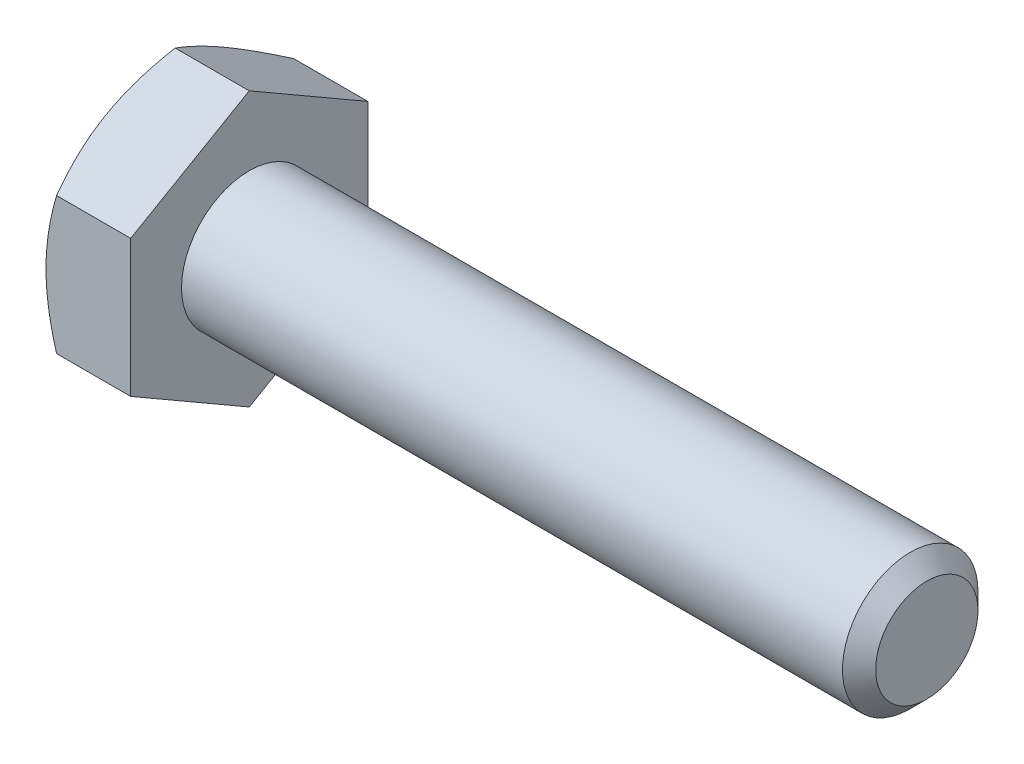
SolidWorks part; units mm, degrees
material "Alloy Steel"
ref_plane "Front Plane" through (0, 0, 0) normal (0, 0, 1) x (1, 0, 0)
ref_plane "Top Plane" through (0, 0, 0) normal (0, 1, 0) x (1, 0, 0)
ref_plane "Right Plane" through (0, 0, 0) normal (1, 0, 0) x (0, 0, -1)
sketch "Sketch1" plane through (0, 0, 0) normal (0, 0, 1) x (1, 0, 0)
  line L0 (-17.8594, 0) -> (17.8594, 0) construction
  line L1 (17.8594, 3.175) -> (17.8594, -3.175) construction
  line L2 (-13.8906, 5.5562) -> (-13.8906, -5.5562) construction
  line L3 (-17.8594, 5.5562) -> (-17.8594, -5.5562) construction
  point P9 (-13.8906, 0)
  point P10 (13.4144, -3.175)
  dimension "D1" = 4.445
  dimension "Screw Dia" = 6.35
  dimension "Hex" = 11.1125
  dimension "Head Ht" = 3.9688
  dimension "Screw Lenght" = 31.75
ref_plane "Plane2" through (17.8594, 0, 0) normal (1, 0, 0) x (0, 0, -1)
sketch "Sketch5" plane through (17.8594, 0, 0) normal (1, 0, 0) x (0, 0, -1)
  circle A0 centre (0, 0) radius 3.175
extrude "Boss-Extrude3" add sketch "Sketch5" against normal up to vertex (31.75 mm away) up to point (-13.8906, 0, 0)
sketch "Sketch9" plane through (17.8594, 0, 0) normal (1, 0, 0) x (0, 0, -1)
  circle A1 centre (0, 0) radius 3.175
  circle A2 centre (0, 0) radius 3.175
  dimension "D1" = 0
curve "Helix/Spiral1" pitch 1.27 height 33.02 turns 26 parameters "Pitch"=1.27
chamfer "Chamfer1" distance 0.7772 angle 45 1 edges at (17.8594, 0, -3.175)
sketch "Sketch10" plane through (0, 0, 0) normal (0, 0, 1) x (1, 0, 0)
  line L0 (17.8594, 3.175) -> (18.3356, 2.3501)
  line L1 (18.3356, 2.3501) -> (18.4944, 2.3501)
  line L2 (18.4944, 2.3501) -> (18.9706, 3.175)
  line L3 (17.8594, 3.175) -> (18.9706, 3.175)
  line L4 (18.415, 3.175) -> (18.415, 2.3501) construction
  line L5 (18.0975, 2.7626) -> (18.7325, 2.7626) construction
  dimension "D1" = 60
  dimension "D2" = 0.1588
  dimension "D3" = 0.635
sketch "Sketch6" plane through (-13.8906, 0, 0) normal (-1, 0, 0) x (0, 0, 1)
  line L0 (0, 5.5562) -> (0, -5.5562) construction
  line L1 (5.5563, 3.2079) -> (0, 6.4158)
  line L2 (0, 6.4158) -> (-5.5562, 3.2079)
  line L3 (-5.5562, 3.2079) -> (-5.5562, -3.2079)
  line L4 (-5.5562, -3.2079) -> (0, -6.4158)
  line L5 (0, -6.4158) -> (5.5563, -3.2079)
  line L6 (5.5563, -3.2079) -> (5.5563, 3.2079)
  circle A0 centre (0, 0) radius 5.5563 construction
extrude "Boss-Extrude4" add sketch "Sketch6" along normal up to vertex (3.9688 mm away) up to point (-17.8594, -5.5562, 0)
sketch "Sketch7" plane through (-17.8594, 0, 0) normal (-1, 0, 0) x (0, 0, 1)
  circle A0 centre (0, 0) radius 5.5563 construction
  circle A1 centre (0, 0) radius 5.5563
sketch "Sketch8" plane through (-17.8594, 0, 0) normal (-1, 0, 0) x (0, 0, 1)
  circle A0 centre (0, 0) radius 5.5563 construction
  circle A1 centre (0, 0) radius 5.5563
extrude "Cut-Extrude3" cut sketch "Sketch8" against normal through all draft 60 flip side to cut
sketch "Sketch12" plane through (-17.8594, 0, 0) normal (-1, 0, 0) x (0, 0, 1)
  line L0 (0, 4.2783) -> (0, 2.3892) construction
  line L1 (0.1667, 4.2783) -> (0.1667, 2.3892)
  line L2 (-0.1667, 4.2783) -> (-0.1667, 2.3892)
  line L3 (0, 3.175) -> (0, -3.175) construction
  arc A0 (0.1667, 4.2783) -> (-0.1667, 4.2783) centre (0, 4.2783) ccw
  arc A1 (-0.1667, 2.3892) -> (0.1667, 2.3892) centre (0, 2.3892) ccw
  circle A3 centre (0, 0) radius 2.2225 construction
  circle A4 centre (0, 0) radius 4.445 construction
  point P2 (0, 3.3337)
  dimension "D1" = 4.445
  dimension "D3" = 8.89
  dimension "D2" = 0.3334
extrude "Cut-Extrude4" cut sketch "Sketch12" against normal blind 0.254
pattern_circular "CirPattern1" count 3 over 360 about axis through (0, 0, 0) along (1, 0, 0) of "Cut-Extrude4"
equation "\"D2@Sketch10\" = \"Pitch@Helix/Spiral1\"*.125"
equation "\"D3@Sketch10\" = \"Pitch@Helix/Spiral1\"*.5"
equation "\"D1@Chamfer1\" = \"Pitch@Helix/Spiral1\"*.612"
equation "\"D1@Sketch12\" = \"Hex@Sketch1\"*.4"
equation "\"D3@Sketch12\" = \"Hex@Sketch1\"*.8"
equation "\"D2@Sketch12\" = \"Hex@Sketch1\"*.03"
equation "\"D1@Sketch1\" = \"Pitch@Helix/Spiral1\"*3.5"
equation "\"D3@Helix/Spiral1\" = \"Screw Lenght@Sketch1\"+\"Pitch@Helix/Spiral1\""
